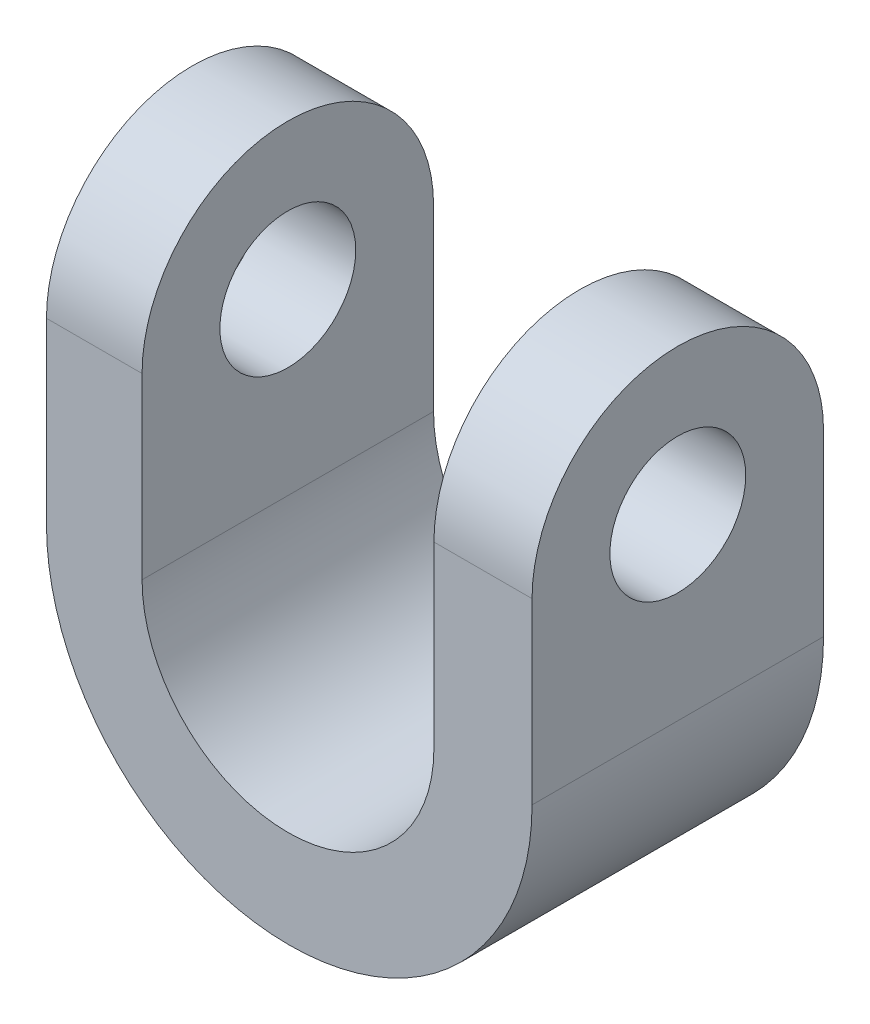
SolidWorks part; units mm, degrees
ref_plane "Front Plane" through (0, 0, 0) normal (0, 0, 1) x (1, 0, 0)
ref_plane "Top Plane" through (0, 0, 0) normal (0, 1, 0) x (1, 0, 0)
ref_plane "Right Plane" through (0, 0, 0) normal (1, 0, 0) x (0, 0, -1)
sketch "Sketch1" plane through (0, 0, 0) normal (0, 0, 1) x (1, 0, 0)
  line L0 (40.0883, 44.2733) -> (40.0883, -18.282)
  line L1 (-44.9341, -18.282) -> (-44.9341, 44.2733)
  line L2 (-44.9341, 44.2733) -> (-28.194, 44.2733)
  line L3 (-28.194, 44.2733) -> (-28.194, -18.282)
  line L4 (22.9076, -18.282) -> (22.9076, 44.2733)
  line L5 (22.9076, 44.2733) -> (40.0883, 44.2733)
  arc A0 (40.0883, -18.282) -> (-44.9341, -18.282) centre (-2.4229, -18.282) cw
  arc A1 (-28.194, -18.282) -> (22.9076, -18.282) centre (-2.6432, -18.282) ccw
extrude "Boss-Extrude1" add sketch "Sketch1" against normal blind 80
sketch "Sketch2" plane through (40.0883, 0, 0) normal (1, 0, 0) x (0, 0, -1)
  line L0 (14.4814, 12.9957) -> (14.4814, -18.282)
  line L1 (80, -18.282) -> (0, -18.282) construction
  line L2 (14.4814, -18.282) -> (65.5186, -18.282)
  line L3 (65.5186, -18.282) -> (65.5186, 12.9957)
  line L4 (14.4814, -18.282) -> (0, -18.282)
  line L5 (0, -18.282) -> (0, 44.2733)
  line L6 (0, 44.2733) -> (80, 44.2733)
  line L7 (80, 44.2733) -> (80, -18.282)
  line L8 (80, -18.282) -> (65.5186, -18.282)
  arc A0 (65.5186, 12.9957) -> (14.4814, 12.9957) centre (40, 12.9957) ccw
  circle A1 centre (40, 12.9957) radius 12.7947
  line M2 (0, 44.2733) -> (0, -18.282)
  line M3 (0, -18.282) -> (80, -18.282)
  line M4 (80, -18.282) -> (80, 44.2733)
  line M5 (80, 44.2733) -> (0, 44.2733)
extrude "Cut-Extrude4" cut sketch "Sketch2" against normal through all contours A0 L3 L0 M3 M4 M5 M2
sketch "Sketch3" plane through (0, 0, 0) normal (0, 1, 0) x (1, 0, 0)
  line L0 (-44.9341, 14.4814) -> (40.0883, 14.4814)
  line L1 (40.0883, 14.4814) -> (40.0883, 65.5186) construction
  line L2 (22.9076, 14.4814) -> (40.0883, 14.4814) construction
  line L3 (40.0883, 14.4814) -> (40.0883, 0)
  line L4 (40.0883, 0) -> (40.0883, 14.4814) construction
  line L5 (40.0883, 0) -> (-44.9341, 0)
  line L6 (-44.9341, 0) -> (-44.9341, 14.4814)
  line L7 (-44.9341, 80) -> (40.0883, 80)
  line L8 (40.0883, 80) -> (40.0883, 65.5186)
  line L9 (40.0883, 65.5186) -> (-44.9341, 65.5186)
  line L10 (-44.9341, 65.5186) -> (-44.9341, 80)
extrude "Cut-Extrude5" cut sketch "Sketch3" against normal through all contours L10 L7 L8 L9 | L6 L0 L3 L5
sketch "Sketch4" plane through (40.0883, 0, 0) normal (1, 0, 0) x (0, 0, -1)
  circle A0 centre (40, 12.9957) radius 11.8939
extrude "Cut-Extrude6" cut sketch "Sketch4" against normal through all
